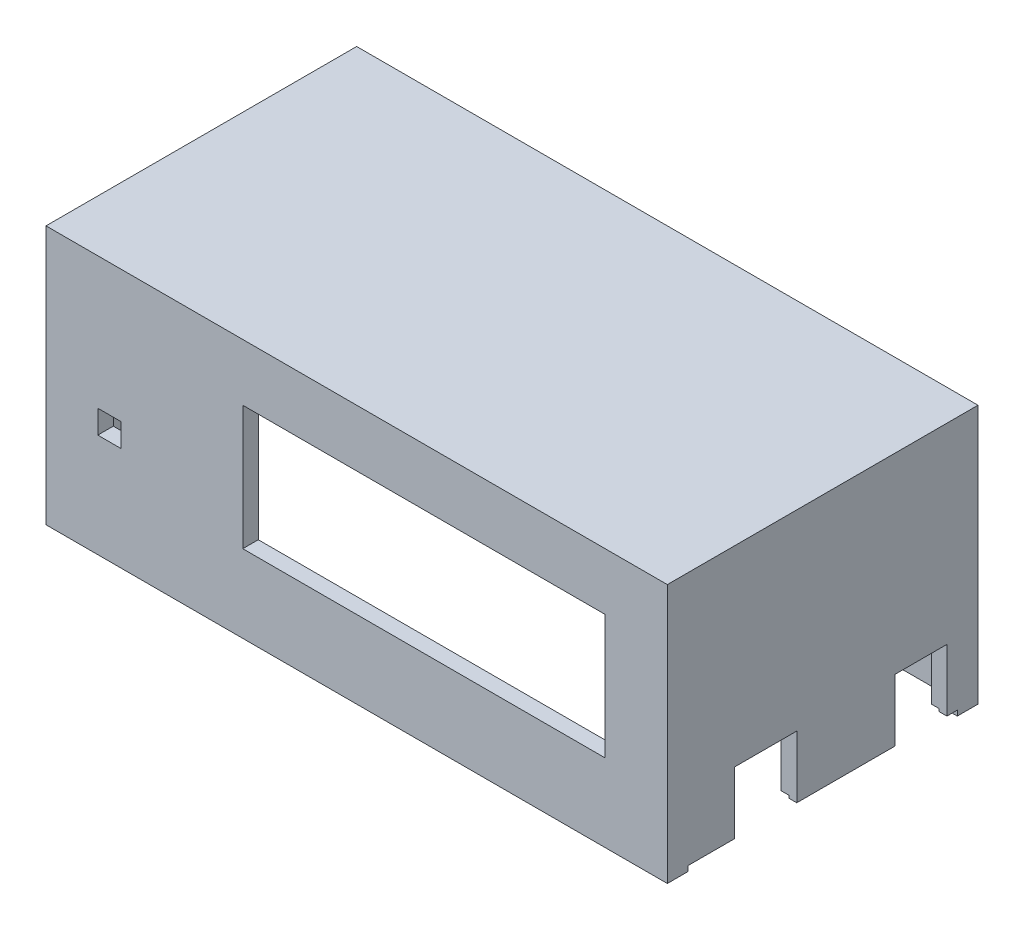
SolidWorks part; units mm, degrees
ref_plane "Front Plane" through (0, 0, 0) normal (0, 0, 1) x (1, 0, 0)
ref_plane "Top Plane" through (0, 0, 0) normal (0, 1, 0) x (1, 0, 0)
ref_plane "Right Plane" through (0, 0, 0) normal (1, 0, 0) x (0, 0, -1)
sketch "Sketch1" plane through (0, 0, 0) normal (0, 1, 0) x (1, 0, 0)
  line L1 (-60, -30) -> (60, -30)
  line L2 (-60, -30) -> (-60, 30)
  line L3 (-60, 30) -> (60, 30)
  line L4 (60, -30) -> (60, 30)
  line L5 (-60, -30) -> (60, 30) construction
  line L6 (-60, 30) -> (60, -30) construction
  point P0 (0, 0)
  dimension "D1" = 120
  dimension "D2" = 60
extrude "Boss-Extrude1" add sketch "Sketch1" along normal blind 50
sketch "Sketch2" plane through (0, 0, 0) normal (0, -1, 0) x (1, 0, 0)
  line L0 (-60, -30) -> (-60, 30) construction
  line L1 (-57, -27) -> (57, -27)
  line L2 (-57, -27) -> (-57, 27)
  line L3 (-57, 27) -> (57, 27)
  line L4 (57, -27) -> (57, 27)
  line L5 (-57, -27) -> (57, 27) construction
  line L6 (-57, 27) -> (57, -27) construction
  line L7 (-60, 30) -> (60, 30) construction
  point P0 (0, 0)
  dimension "D1" = 3
  dimension "D2" = 3
extrude "Cut-Extrude1" cut sketch "Sketch2" against normal blind 47
sketch "Sketch5" plane through (0, 0, 30) normal (0, 0, 1) x (1, 0, 0)
  line L0 (60, 50) -> (60, 0) construction
  line L1 (-22, 39) -> (48, 39)
  line L2 (-22, 39) -> (-22, 15)
  line L3 (-22, 15) -> (48, 15)
  line L4 (48, 39) -> (48, 15)
  line L5 (-22, 39) -> (48, 15) construction
  line L6 (-22, 15) -> (48, 39) construction
  line L7 (-60, 0) -> (60, 0) construction
  point P0 (13, 27)
  dimension "D1" = 70
  dimension "D2" = 24
  dimension "D3" = 12
  dimension "D4" = 15
extrude "Cut-Extrude3" cut sketch "Sketch5" against normal blind 7
sketch "Sketch6" plane through (0, 0, 30) normal (0, 0, 1) x (1, 0, 0)
  line L0 (-60, 50) -> (-60, 0) construction
  line L1 (-50, 24.5) -> (-45.5, 24.5)
  line L2 (-50, 24.5) -> (-50, 20)
  line L3 (-50, 20) -> (-45.5, 20)
  line L4 (-45.5, 24.5) -> (-45.5, 20)
  line L5 (-50, 24.5) -> (-45.5, 20) construction
  line L6 (-50, 20) -> (-45.5, 24.5) construction
  line L7 (-60, 0) -> (60, 0) construction
  point P0 (-47.75, 22.25)
  dimension "D1" = 4.5
  dimension "D2" = 4.5
  dimension "D3" = 10
  dimension "D4" = 20
extrude "Cut-Extrude4" cut sketch "Sketch6" against normal blind 7
sketch "Sketch7" plane through (60, 0, 0) normal (1, 0, 0) x (0, 0, -1)
  line L0 (-30, 0) -> (30, 0) construction
  line L1 (-17, 13) -> (-5, 13)
  line L2 (-17, 13) -> (-17, 0)
  line L3 (-17, 0) -> (-5, 0)
  line L4 (-5, 13) -> (-5, 0)
  line L5 (-17, 13) -> (-5, 0) construction
  line L6 (-17, 0) -> (-5, 13) construction
  line L7 (14, 13) -> (24, 13)
  line L8 (14, 13) -> (14, 0)
  line L9 (14, 0) -> (24, 0)
  line L10 (24, 13) -> (24, 0)
  line L11 (14, 13) -> (24, 0) construction
  line L12 (14, 0) -> (24, 13) construction
  line L13 (30, 50) -> (30, 0) construction
  point P0 (-11, 6.5)
  point P5 (19, 6.5)
  dimension "D1" = 13
  dimension "D2" = 12
  dimension "D3" = 13
  dimension "D4" = 10
  dimension "D5" = 19
  dimension "D6" = 6
extrude "Cut-Extrude5" cut sketch "Sketch7" against normal blind 3
sketch "Sketch8" plane through (60, 0, 0) normal (1, 0, 0) x (0, 0, -1)
  line L0 (24, 0) -> (30, 0) construction
  line L1 (-26, 1) -> (26, 1)
  line L2 (-26, 1) -> (-26, -1)
  line L3 (-26, -1) -> (26, -1)
  line L4 (26, 1) -> (26, -1)
  line L5 (-26, 1) -> (26, -1) construction
  line L6 (-26, -1) -> (26, 1) construction
  point P0 (0, 0)
  dimension "D1" = 52
  dimension "D2" = 1
extrude "Cut-Extrude6" cut sketch "Sketch8" against normal blind 13
sketch "Sketch9" plane through (0, 0, 0) normal (0, -1, 0) x (1, 0, 0)
  line L0 (-60, 30) -> (60, 30) construction
  line L1 (-58.5, 28.5) -> (58.5, 28.5)
  line L2 (-58.5, 28.5) -> (-58.5, -28.5)
  line L3 (-58.5, -28.5) -> (58.5, -28.5)
  line L4 (58.5, 28.5) -> (58.5, -28.5)
  line L5 (-58.5, 28.5) -> (58.5, -28.5) construction
  line L6 (-58.5, -28.5) -> (58.5, 28.5) construction
  line L7 (-60, -30) -> (-60, 30) construction
  point P0 (0, 0)
  dimension "D1" = 1.5
  dimension "D2" = 1.5
extrude "Cut-Extrude7" cut sketch "Sketch9" against normal blind 1.5
sketch "Sketch10" plane through (0, 0, -30) normal (0, 0, -1) x (-1, 0, 0)
  line L0 (-60, 0) -> (60, 0) construction
  line L1 (-4, 16) -> (4, 16)
  line L2 (-4, 16) -> (-4, 8)
  line L3 (-4, 8) -> (4, 8)
  line L4 (4, 16) -> (4, 8)
  line L5 (-4, 16) -> (4, 8) construction
  line L6 (-4, 8) -> (4, 16) construction
  point P0 (0, 12)
  point P7 (0, 0)
  dimension "D1" = 8
  dimension "D2" = 8
  dimension "D3" = 12
extrude "Cut-Extrude8" cut sketch "Sketch10" against normal blind 11.5
